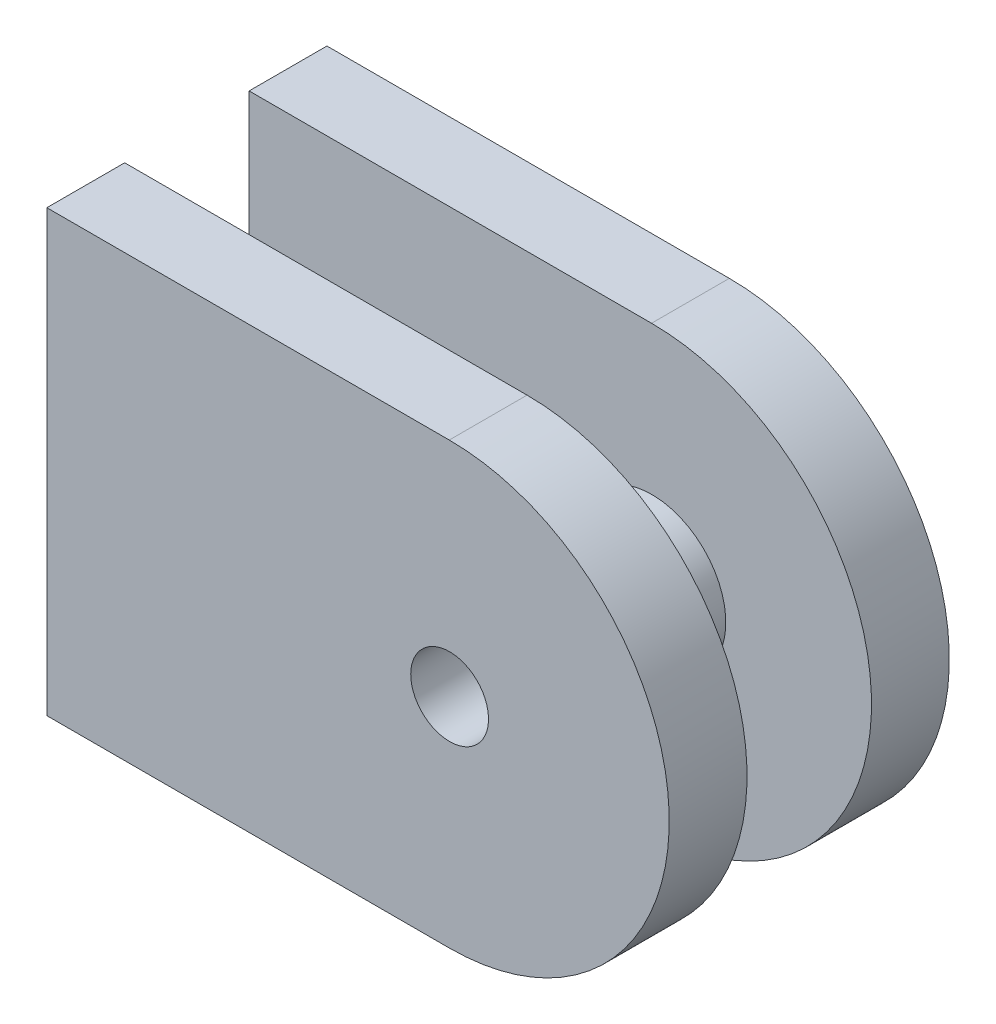
SolidWorks part; units mm, degrees
ref_plane "Front Plane" through (0, 0, 0) normal (0, 0, 1) x (1, 0, 0)
ref_plane "Top Plane" through (0, 0, 0) normal (0, 1, 0) x (1, 0, 0)
ref_plane "Right Plane" through (0, 0, 0) normal (1, 0, 0) x (0, 0, -1)
sketch "Sketch2" plane through (0, 0, 0) normal (0, 0, 1) x (1, 0, 0)
  line L1 (0, 0) -> (40, 0)
  line L2 (0, 0) -> (0, 35)
  line L3 (0, 35) -> (40, 35)
  line L4 (40, 0) -> (40, 35)
  dimension "D1" = 35
  dimension "D2" = 40
extrude "Boss-Extrude1" add sketch "Sketch2" along normal blind 5
ref_plane "Plane1" through (0, 0, 9) normal (0, 0, 1) x (1, 0, 0)
sketch "Sketch4" plane through (0, 0, 5) normal (0, 0, 1) x (1, 0, 0)
  line L0 (20.6805, 17.5) -> (32.2773, 17.5) construction
  line L1 (25.8854, 30.2962) -> (25.8854, 20.1604) construction
  line L2 (40, 35) -> (0, 35) construction
  line L3 (0, 0) -> (40, 0) construction
  circle A0 centre (25.8854, 17.5) radius 4.75
  dimension "D1" = 9.5
extrude "Boss-Extrude2" add sketch "Sketch4" along normal blind 8
mirror "Mirror4" about plane through (0, 0, 9) normal (0, 0, 1) of bodies 105 101
sketch "Sketch6" plane through (0, 0, 5) normal (0, 0, 1) x (1, 0, 0)
  line L0 (25.8627, 31.7713) -> (0, 31.7713)
  line L1 (0, 35) -> (0, 0) construction
  line L2 (25.8627, 3.4967) -> (0, 3.4967)
  line L3 (0, 3.4967) -> (0, 31.7713)
  arc A0 (25.8627, 3.4967) -> (25.8627, 31.7713) centre (25.8627, 17.634) ccw
extrude "Cut-Extrude2" cut sketch "Sketch6" against normal blind 20 and the other way blind 20 flip side to cut
sketch "Sketch8" plane through (0, 0, 0) normal (0, 0, -1) x (-1, 0, 0)
  point P0 (-25.8854, 17.5)
hole_wizard "M6x1.0 Tapped Hole1" positions "Sketch9" profile "Sketch10" tap size "M6x1.0" standard "BSI" end condition through all
sketch "Sketch9" plane through (0, 0, 0) normal (0, 0, -1) x (-1, 0, 0)
  point P0 (-25.8854, 17.5)
sketch "Sketch10" plane through (25.8854, 17.5, 0) normal (1, 0, 0) x (0, 1, 0)
  line L0 (0, 0) -> (0, 18)
  line L1 (0, 18) -> (2.5, 18)
  line L2 (2.5, 18) -> (2.5, 0)
  line L5 (2.5, 0) -> (0, 0)
  line L11 (0, -6.35) -> (0, 107.95) construction
  dimension "Thru Tap Drill Dia." = 5
  dimension "Thru Tap Drill Depth" = 18
cosmetic thread "Hole Thread1" parameters "D2"=6
